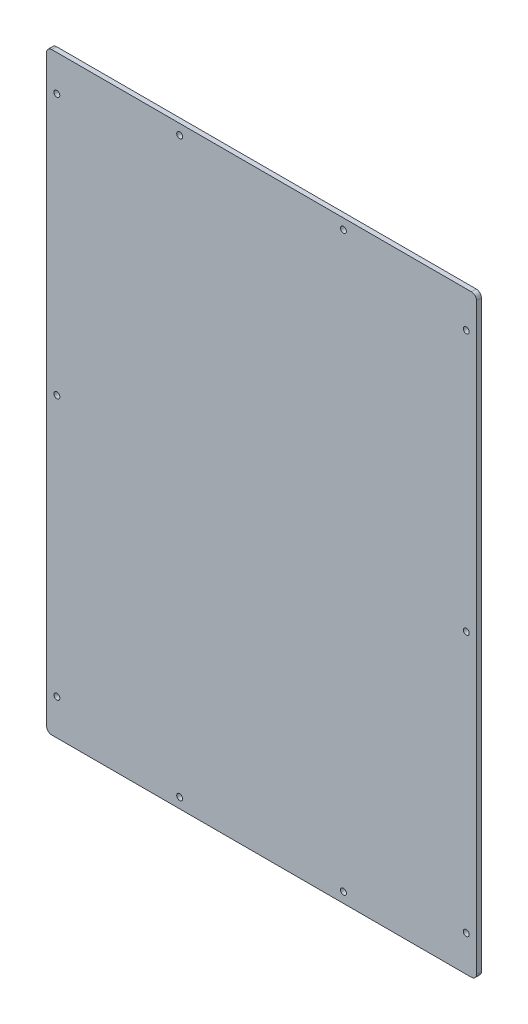
SolidWorks part; units mm, degrees
ref_plane "Front Plane" through (0, 0, 0) normal (0, 0, 1) x (1, 0, 0)
ref_plane "Top Plane" through (0, 0, 0) normal (0, 1, 0) x (1, 0, 0)
ref_plane "Right Plane" through (0, 0, 0) normal (1, 0, 0) x (0, 0, -1)
sketch "Sketch1" plane through (0, 0, 0) normal (0, 0, 1) x (1, 0, 0)
  line L0 (55, 0) -> (-55, 0) construction
  line L1 (210, -290) -> (-210, -290)
  line L2 (210, -290) -> (210, 290)
  line L3 (210, 290) -> (-210, 290)
  line L4 (-210, -290) -> (-210, 290)
  line L5 (0, 0) -> (-210, 0) construction
  line L6 (0, 0) -> (210, 0) construction
  line L7 (0, -55) -> (0, 55) construction
  point P0 (0, 0)
  point P6 (-207.7848, 4.5675)
  point P7 (-207.7848, -15)
  point P19 (-207.7848, -4.5675)
  point P22 (207.7848, -15)
  point P23 (207.7848, -4.5675)
  point P24 (207.7848, 4.5675)
  dimension "D1" = 420
  dimension "D2" = 580
  dimension "D3" = 2.2152
extrude "Boss-Extrude1" add sketch "Sketch1" along normal blind 4.7625
sketch "Sketch2" plane through (0, 0, 4.7625) normal (0, 0, 1) x (1, 0, 0)
  line L0 (210, 290) -> (-210, 290) construction
  line L1 (-210, 290) -> (-210, -290) construction
  line L2 (0, -55) -> (0, 55) construction
  line L3 (55, 0) -> (-55, 0) construction
  line L4 (-210, -290) -> (210, -290) construction
  point P0 (-200, 255)
  point P1 (-200, 0)
  point P2 (-80, 280)
  point P4 (80, 280)
  point P9 (80, -280)
  point P12 (200, 255)
  point P13 (200, 0)
  point P14 (-80, -280)
  point P18 (200, -255)
  point P19 (-200, -255)
  dimension "D1" = 35
  dimension "D2" = 10
  dimension "D3" = 10
  dimension "D4" = 10
  dimension "D5" = 10
  dimension "D6" = 10
  dimension "D7" = 80
  dimension "D8" = 80
hole_wizard "M5 Clearance Hole1" positions "Sketch3" profile "Sketch4" hole size "M5" standard "ANSI Metric" end condition through all
sketch "Sketch3" plane through (0, 0, 4.7625) normal (0, 0, 1) x (1, 0, 0)
  point P0 (-200, 255)
  point P3 (-200, 0)
  point P6 (-200, -255)
  point P9 (200, 255)
  point P12 (200, 0)
  point P15 (200, -255)
  point P19 (-80, 280)
  point P22 (80, 280)
  point P25 (80, -280)
  point P28 (-80, -280)
sketch "Sketch4" plane through (-200, 255, 4.7625) normal (1, 0, 0) x (0, -1, 0)
  line L0 (0, 0) -> (0, 4.7625)
  line L1 (0, 4.7625) -> (2.9, 4.7625)
  line L2 (2.9, 4.7625) -> (2.9, 0)
  line L5 (2.9, 0) -> (0, 0)
  line L11 (0, -6.35) -> (0, 107.95) construction
  dimension "Thru Hole Dia." = 5.8
  dimension "Thru Hole Depth" = 4.7625
fillet "Fillet1" radius 5 4 edges at (210, 290, 2.3813) (210, -290, 2.3813) (-210, -290, 2.3813) (-210, 290, 2.3813)
